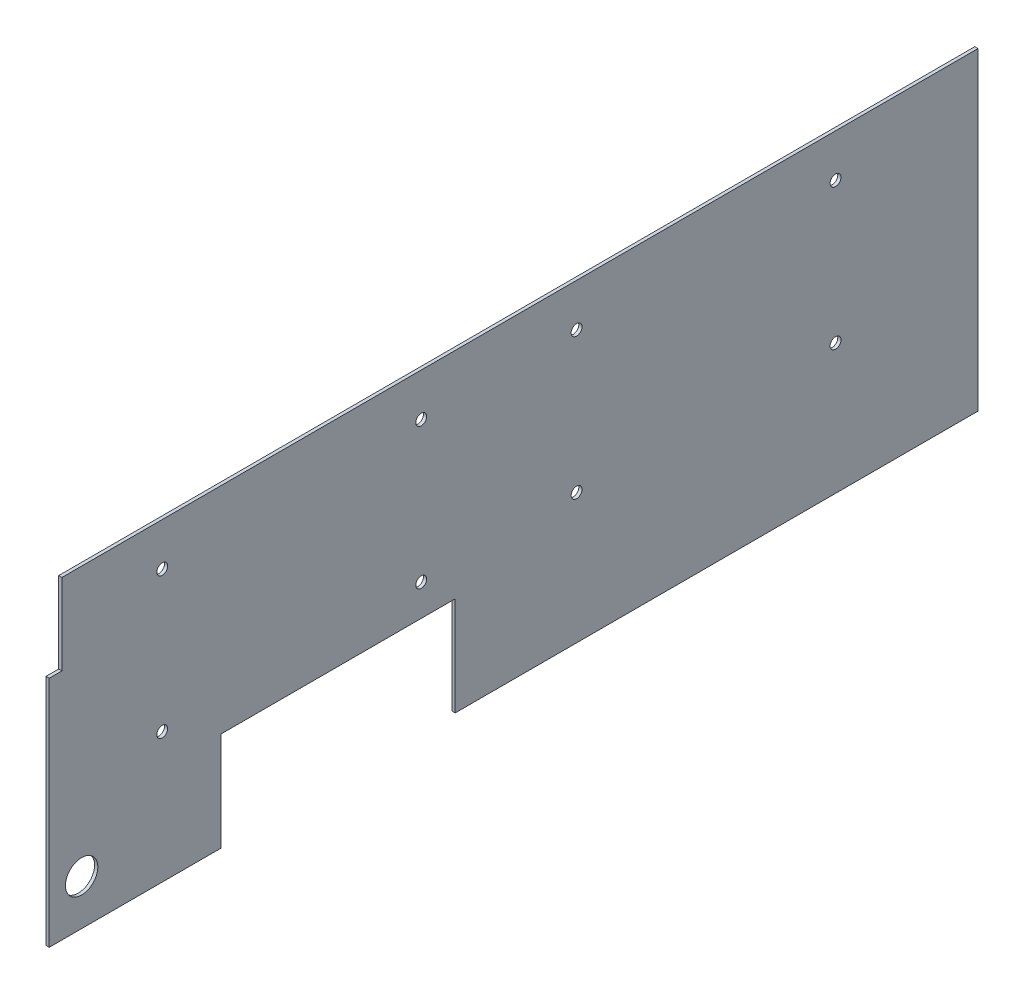
SolidWorks part; units mm, degrees
ref_plane "Front Plane" through (0, 0, 0) normal (0, 0, 1) x (1, 0, 0)
ref_plane "Top Plane" through (0, 0, 0) normal (0, 1, 0) x (1, 0, 0)
ref_plane "Right Plane" through (0, 0, 0) normal (1, 0, 0) x (0, 0, -1)
sketch "Sketch1" plane through (0, 0, 0) normal (1, 0, 0) x (0, 0, -1)
  line L1 (-227.7341, -76.9938) -> (227.7341, -76.9938)
  line L2 (-227.7341, -76.9938) -> (-227.7341, 76.9938)
  line L3 (-227.7341, 76.9938) -> (227.7341, 76.9938)
  line L4 (227.7341, -76.9938) -> (227.7341, 76.9938)
  line L5 (-227.7341, -76.9938) -> (227.7341, 76.9938) construction
  line L6 (-227.7341, 76.9938) -> (227.7341, -76.9938) construction
  point P0 (0, 0)
  dimension "D1" = 153.9875
  dimension "D2" = 455.4682
extrude "Boss-Extrude1" add sketch "Sketch1" along normal blind 1.5875
sketch "Sketch2" plane through (0, 0, 0) normal (-1, 0, 0) x (0, 0, 1)
  line L0 (221.5284, 37.3063) -> (221.5284, -76.9938)
  line L1 (227.7341, 76.9938) -> (221.5284, 76.9938)
  line L2 (227.7341, 76.9938) -> (227.7341, 37.3062)
  line L3 (227.7341, 37.3062) -> (221.5284, 37.3063)
  line L4 (221.5284, 76.9938) -> (221.5284, 37.3063)
  line L5 (227.7341, -76.9938) -> (-227.7341, -76.9938) construction
  line L6 (221.5284, 37.3063) -> (-227.7341, 37.3062)
  line L7 (-227.7341, -76.9938) -> (-227.7341, 76.9938) construction
  line L8 (143.5966, -28.5169) -> (227.7341, -28.5169)
  line L9 (143.5966, -76.9938) -> (28.6472, -76.9938)
  line L10 (143.5966, -76.9938) -> (143.5966, -28.5169)
  line L11 (143.5966, -28.5169) -> (28.6472, -28.5169)
  line L12 (28.6472, -76.9938) -> (28.6472, -28.5169)
  line L13 (227.7341, 76.9938) -> (227.7341, -76.9938) construction
  line L14 (28.6472, -28.5169) -> (-227.7341, -28.5169)
  line L15 (143.5966, -28.5169) -> (143.5966, 76.9938)
  line L16 (-227.7341, 76.9938) -> (227.7341, 76.9938) construction
  line L17 (-227.7341, -76.9938) -> (211.8591, -76.9937)
  line L18 (211.8591, -76.9937) -> (211.8591, -54.7687)
  circle A0 centre (211.8591, -54.7687) radius 7.9375
  dimension "D3" = 15.875
  dimension "D1" = 439.5932
  dimension "D2" = 22.225
extrude "Cut-Extrude1" cut sketch "Sketch2" against normal up to surface (1.5875 mm away)
sketch "Sketch3" plane through (1.5875, 0, 0) normal (1, 0, 0) x (0, 0, -1)
  line L0 (227.7341, 76.9938) -> (227.7341, 55.9594)
  line L1 (227.7341, -76.9938) -> (227.7341, 76.9938) construction
  line L2 (227.7341, 55.9594) -> (157.8841, 55.9594)
  line L3 (157.8841, 55.9594) -> (30.8841, 55.9594)
  line L4 (30.8841, 55.9594) -> (-45.3159, 55.9594)
  line L5 (-45.3159, 55.9594) -> (-172.3159, 55.9594)
  line L6 (-172.3159, 55.9594) -> (-172.3159, -13.0969)
  line L7 (-172.3159, -13.0969) -> (-45.3159, -13.0969)
  line L8 (-45.3159, -13.0969) -> (30.8841, -13.0969)
  line L9 (30.8841, -13.0969) -> (157.8841, -13.0969)
  circle A0 centre (-172.3159, 55.9594) radius 2.667
  circle A1 centre (-172.3159, -13.0969) radius 2.667
  circle A2 centre (-45.3159, -13.0969) radius 2.667
  circle A3 centre (-45.3159, 55.9594) radius 2.667
  circle A4 centre (30.8841, 55.9594) radius 2.667
  circle A5 centre (30.8841, -13.0969) radius 2.667
  circle A6 centre (157.8841, 55.9594) radius 2.667
  circle A7 centre (157.8841, -13.0969) radius 2.667
  dimension "D10" = 5.334
  dimension "D11" = 5.334
  dimension "D1" = 21.0344
  dimension "D2" = 69.85
  dimension "D3" = 127
  dimension "D4" = 76.2
  dimension "D5" = 127
  dimension "D6" = 69.0563
  dimension "D7" = 127
  dimension "D8" = 76.2
  dimension "D9" = 127
  dimension "D12" = 2
  dimension "D13" = 2
  dimension "D14" = 2
extrude "Cut-Extrude2" cut sketch "Sketch3" against normal up to surface (1.5875 mm away)
